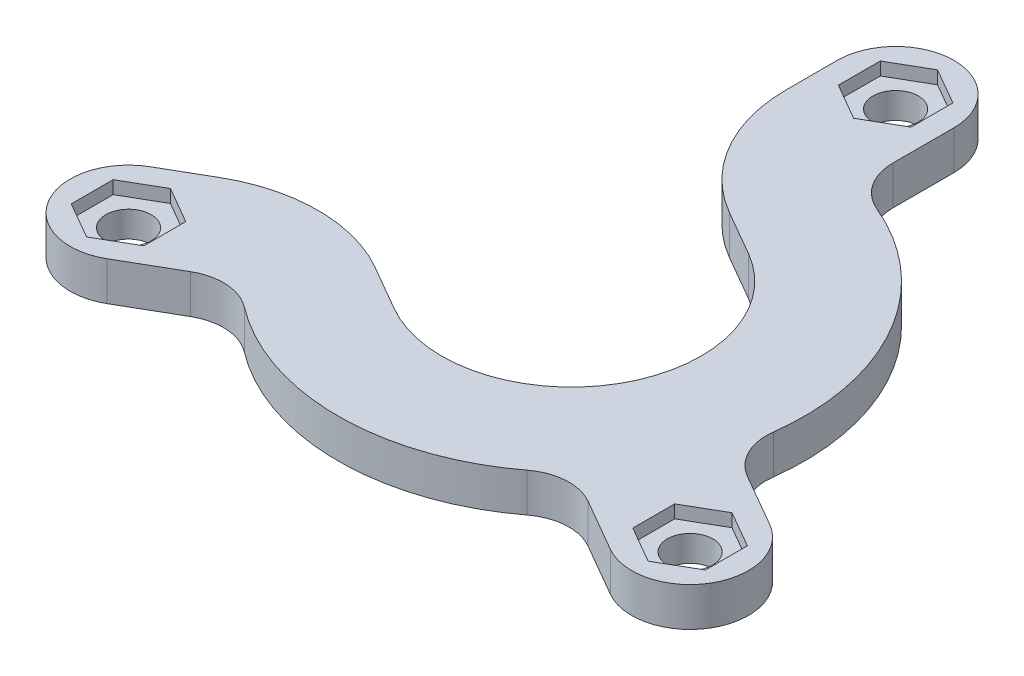
SolidWorks part; units mm, degrees
ref_plane "Front Plane" through (0, 0, 0) normal (0, 0, 1) x (1, 0, 0)
ref_plane "Top Plane" through (0, 0, 0) normal (0, 1, 0) x (1, 0, 0)
ref_plane "Right Plane" through (0, 0, 0) normal (1, 0, 0) x (0, 0, -1)
sketch "Sketch1" plane through (0, 0, 0) normal (0, 1, 0) x (1, 0, 0)
  line L0 (0, 0) -> (0, 9.0907) construction
  line L1 (0, 0) -> (7.1459, -4.1257) construction
  line L2 (0, 0) -> (-8.3205, -4.8039) construction
  line L3 (23.9006, -8.6029) -> (19.8231, -6.2487)
  line L4 (19.4006, -16.3971) -> (15.3231, -14.0429)
  line L5 (-19.4006, -16.3971) -> (-15.3231, -14.0429)
  line L6 (-23.9006, -8.6029) -> (-20.5, -6.6395)
  line L7 (-4.5, 25) -> (-4.5, 21.0733)
  line L8 (4.5, 25) -> (4.5, 20.2916)
  line L9 (-5, -8.6603) -> (-8.5, -6.6395)
  line L10 (-4.5, 25) -> (-4.5, 17.3205) [skipped]
  line L11 (-23.9006, -8.6029) -> (-17.25, -4.7631) [skipped]
  line L12 (5, 8.6603) -> (1.5, 10.681)
  line L13 (-5, -8.6603) -> (0, 0) construction
  line L14 (0, 0) -> (5, 8.6603) construction
  arc A0 (-5, -8.6603) -> (5, 8.6603) centre (0, 0) ccw
  arc A1 (17.8552, -2.2783) -> (6.9545, 16.6022) centre (0, 0) ccw
  circle A2 centre (0, 25) radius 1.75
  circle A3 centre (0, 0) radius 25 construction
  circle A4 centre (21.6506, -12.5) radius 1.75
  circle A5 centre (-21.6506, -12.5) radius 1.75
  arc A6 (19.4006, -16.3971) -> (23.9006, -8.6029) centre (21.6506, -12.5) ccw
  arc A7 (-23.9006, -8.6029) -> (-19.4006, -16.3971) centre (-21.6506, -12.5) ccw
  arc A8 (4.5, 25) -> (-4.5, 25) centre (0, 25) ccw
  arc A9 (-8.5, -6.6395) -> (-20.5, -6.6395) centre (-14.5, -17.0318) ccw
  arc A10 (-10.9007, -14.3239) -> (10.9007, -14.3239) centre (0, 0) ccw
  arc A11 (1.5, 10.681) -> (-4.5, 21.0733) centre (7.5, 21.0733) cw
  arc A12 (-15.3231, -14.0429) -> (-10.9007, -14.3239) centre (-13.3231, -17.507) cw
  arc A13 (15.3231, -14.0429) -> (10.9007, -14.3239) centre (13.3231, -17.507) ccw
  arc A14 (19.8231, -6.2487) -> (17.8552, -2.2783) centre (21.8231, -2.7846) cw
  arc A15 (4.5, 20.2916) -> (6.9545, 16.6022) centre (8.5, 20.2916) ccw
  point P36 (0, 0)
  dimension "D3" = 20
  dimension "D4" = 8
  dimension "D5" = 50
  dimension "D6" = 3.5
  dimension "D7" = 9
  dimension "D9" = 4
  dimension "D10" = 12
  dimension "D1" = 120
  dimension "D2" = 120
  dimension "D8" = 3
extrude "Boss-Extrude1" add sketch "Sketch1" along normal blind 3
sketch "Sketch2" plane through (0, 3, 0) normal (0, 1, 0) x (1, 0, 0)
  line L1 (2.8, 23.3834) -> (2.8, 26.6166)
  line L2 (2.8, 26.6166) -> (0, 28.2332)
  line L3 (0, 28.2332) -> (-2.8, 26.6166)
  line L4 (-2.8, 26.6166) -> (-2.8, 23.3834)
  line L5 (-2.8, 23.3834) -> (0, 21.7668)
  line L6 (0, 21.7668) -> (2.8, 23.3834)
  line L7 (24.4506, -14.1166) -> (24.4506, -10.8834)
  line L8 (24.4506, -10.8834) -> (21.6506, -9.2668)
  line L9 (21.6506, -9.2668) -> (18.8506, -10.8834)
  line L10 (18.8506, -10.8834) -> (18.8506, -14.1166)
  line L11 (18.8506, -14.1166) -> (21.6506, -15.7332)
  line L12 (21.6506, -15.7332) -> (24.4506, -14.1166)
  line L13 (-24.4506, -14.1166) -> (-21.6506, -15.7332)
  line L14 (-21.6506, -15.7332) -> (-18.8506, -14.1166)
  line L15 (-18.8506, -14.1166) -> (-18.8506, -10.8834)
  line L16 (-18.8506, -10.8834) -> (-21.6506, -9.2668)
  line L17 (-21.6506, -9.2668) -> (-24.4506, -10.8834)
  line L18 (-24.4506, -10.8834) -> (-24.4506, -14.1166)
  circle A0 centre (0, 25) radius 2.8 construction
  circle A1 centre (21.6506, -12.5) radius 2.8 construction
  circle A2 centre (-21.6506, -12.5) radius 2.8 construction
  dimension "D1" = 5.6
extrude "Cut-Extrude1" cut sketch "Sketch2" against normal blind 1
